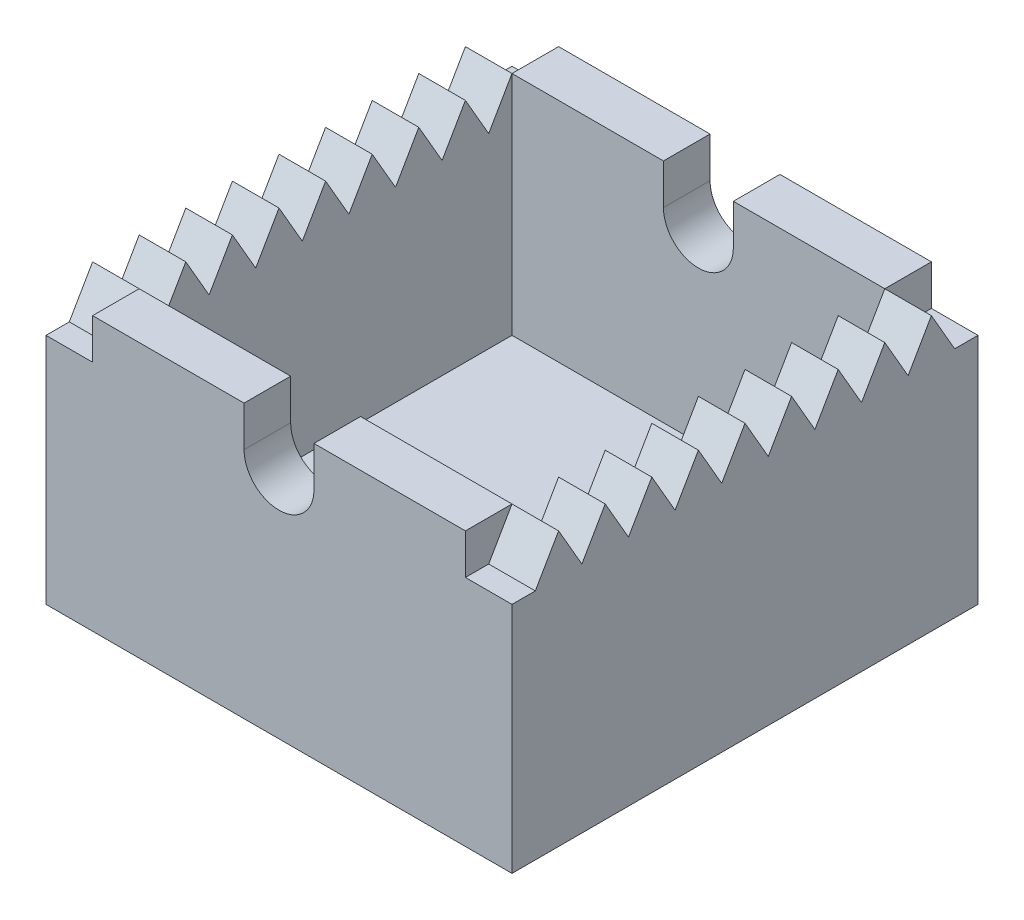
SolidWorks part; units mm, degrees
ref_plane "Front Plane" through (0, 0, 0) normal (0, 0, 1) x (1, 0, 0)
ref_plane "Top Plane" through (0, 0, 0) normal (0, 1, 0) x (1, 0, 0)
ref_plane "Right Plane" through (0, 0, 0) normal (1, 0, 0) x (0, 0, -1)
sketch "Sketch1" plane through (0, 0, 0) normal (0, 1, 0) x (1, 0, 0)
  line L1 (-50, -50) -> (50, -50)
  line L2 (-50, -50) -> (-50, 50)
  line L3 (-50, 50) -> (50, 50)
  line L4 (50, -50) -> (50, 50)
  line L5 (-50, -50) -> (50, 50) construction
  line L6 (-50, 50) -> (50, -50) construction
  line L11 (-40, -40) -> (40, 40) construction
  line L12 (-40, 40) -> (40, -40) construction
  point P0 (0, 0)
  point P6 (0, 0)
  dimension "D1" = 100
extrude "Boss-Extrude1" add sketch "Sketch1" along normal mid plane 50
sketch "Sketch4" plane through (0, 25, 0) normal (0, 1, 0) x (1, 0, 0)
  line L0 (50, 50) -> (-50, 50) construction
  line L1 (-40, -40) -> (40, -40)
  line L2 (-40, -40) -> (-40, 40)
  line L3 (-40, 40) -> (40, 40)
  line L4 (40, -40) -> (40, 40)
  line L5 (-40, -40) -> (40, 40) construction
  line L6 (-40, 40) -> (40, -40) construction
  point P0 (0, 0)
  dimension "D1" = 10
extrude "Cut-Extrude2" cut sketch "Sketch4" against normal offset from surface (40 mm away) 10 from surface at 0 up to face at (0, -25, 0) starting at face at (0, 25, 0)
sketch "Sketch5" plane through (0, 0, 50) normal (0, 0, 1) x (1, 0, 0)
  line L0 (-50, 25) -> (50, 25) construction
  circle A0 centre (0, 25) radius 7.5
  dimension "D1" = 15
extrude "Cut-Extrude3" cut sketch "Sketch5" against normal up to surface (100 mm away) from surface at 0 up to face at (0, 0, -50) starting at face at (0, 0, 50)
sketch "Sketch7" plane through (-50, 0, 0) normal (-1, 0, 0) x (0, 0, 1)
  line L0 (-45, 25) -> (-40, 33.6603)
  line L1 (-40, 33.6603) -> (-35, 25)
  line L2 (-50, 25) -> (50, 25) construction
  line L3 (-35, 25) -> (-45, 25)
  line L4 (-30, 33.6603) -> (-25, 25)
  line L5 (-35, 25) -> (-30, 33.6603)
  line L6 (-25, 25) -> (-35, 25)
  line L7 (-20, 33.6603) -> (-15, 25)
  line L8 (-25, 25) -> (-20, 33.6603)
  line L9 (-15, 25) -> (-25, 25)
  line L10 (-10, 33.6603) -> (-5, 25)
  line L11 (-15, 25) -> (-10, 33.6603)
  line L12 (-5, 25) -> (-15, 25)
  line L13 (0, 33.6603) -> (5, 25)
  line L14 (-5, 25) -> (0, 33.6603)
  line L15 (5, 25) -> (-5, 25)
  line L16 (10, 33.6603) -> (15, 25)
  line L17 (5, 25) -> (10, 33.6603)
  line L18 (15, 25) -> (5, 25)
  line L19 (20, 33.6603) -> (25, 25)
  line L20 (15, 25) -> (20, 33.6603)
  line L21 (25, 25) -> (15, 25)
  line L22 (30, 33.6603) -> (35, 25)
  line L23 (25, 25) -> (30, 33.6603)
  line L24 (35, 25) -> (25, 25)
  line L25 (40, 33.6603) -> (45, 25)
  line L26 (35, 25) -> (40, 33.6603)
  line L27 (45, 25) -> (35, 25)
  dimension "D1" = 10
  dimension "D3" = 5
  dimension "D2" = 9
extrude "Boss-Extrude4" add sketch "Sketch7" against normal up to surface (10 mm away) up to face at (-40, 5, 0)
sketch "Sketch8" plane through (50, 0, 0) normal (1, 0, 0) x (0, 0, -1)
  line L0 (-45, 25) -> (-40, 33.6603)
  line L1 (-40, 33.6603) -> (-35, 25)
  line L2 (-35, 25) -> (-45, 25)
  line L3 (-25, 25) -> (-35, 25)
  line L4 (-35, 25) -> (-30, 33.6603)
  line L5 (-30, 33.6603) -> (-25, 25)
  line L6 (-15, 25) -> (-25, 25)
  line L7 (-25, 25) -> (-20, 33.6603)
  line L8 (-20, 33.6603) -> (-15, 25)
  line L9 (-5, 25) -> (-15, 25)
  line L10 (-15, 25) -> (-10, 33.6603)
  line L11 (-10, 33.6603) -> (-5, 25)
  line L12 (5, 25) -> (-5, 25)
  line L13 (-5, 25) -> (0, 33.6603)
  line L14 (0, 33.6603) -> (5, 25)
  line L15 (15, 25) -> (5, 25)
  line L16 (5, 25) -> (10, 33.6603)
  line L17 (10, 33.6603) -> (15, 25)
  line L18 (25, 25) -> (15, 25)
  line L19 (15, 25) -> (20, 33.6603)
  line L20 (20, 33.6603) -> (25, 25)
  line L21 (35, 25) -> (25, 25)
  line L22 (25, 25) -> (30, 33.6603)
  line L23 (30, 33.6603) -> (35, 25)
  line L24 (45, 25) -> (35, 25)
  line L25 (35, 25) -> (40, 33.6603)
  line L26 (40, 33.6603) -> (45, 25)
  line L30 (-45, 25) -> (-40, 33.6603) construction
  line L31 (-50, 25) -> (50, 25) construction
  line M33 (50, 25) -> (-50, 25)
  dimension "D2" = 10
  dimension "D1" = 9
extrude "Boss-Extrude5" add sketch "Sketch8" against normal up to surface (10 mm away) contours L1 L0 M33 | L5 L4 M33 | L8 L7 M33 | L11 L10 M33 | L14 L13 M33 | L17 L16 M33 | L20 L19 M33 | L23 L22 M33 | L26 L25 M33 up to face at (40, 5, 0)
sketch "Sketch9" plane through (0, 0, 50) normal (0, 0, 1) x (1, 0, 0)
  line L0 (-40, 25) -> (-40, 33.6603) construction
  line L1 (-40, 25) -> (-7.5, 25)
  line L2 (-40, 25) -> (-40, 33.6603)
  line L3 (-40, 33.6603) -> (-7.5, 33.6603)
  line L4 (-7.5, 25) -> (-7.5, 33.6603)
  line L5 (7.5, 25) -> (40, 25)
  line L6 (7.5, 25) -> (7.5, 33.6603)
  line L7 (7.5, 33.6603) -> (40, 33.6603)
  line L8 (40, 25) -> (40, 33.6603)
  line L9 (-40, 33.6603) -> (-50, 33.6603) construction
  point P11 (0, 0)
  point P13 (0, 0)
  point P15 (0, 0)
  point P16 (0, 0)
extrude "Boss-Extrude6" add sketch "Sketch9" against normal up to surface (10 mm away) from surface at -90 up to face at (0, 7.0833, -50) starting at face at (0, 10.4167, -40)
sketch "Sketch11" plane through (0, 0, 50) normal (0, 0, 1) x (1, 0, 0)
  line L1 (-40, 25) -> (-7.5, 25)
  line L2 (-40, 25) -> (-40, 33.6603)
  line L3 (-40, 33.6603) -> (-7.5, 33.6603)
  line L4 (-7.5, 25) -> (-7.5, 33.6603)
  line L5 (7.5, 25) -> (40, 25)
  line L6 (7.5, 25) -> (7.5, 33.6603)
  line L7 (7.5, 33.6603) -> (40, 33.6603)
  line L8 (40, 25) -> (40, 33.6603)
extrude "Boss-Extrude8" add sketch "Sketch11" against normal up to surface (10 mm away) from surface at 0 up to face at (0, 10.4167, 40) starting at face at (0, 7.0833, 50)
